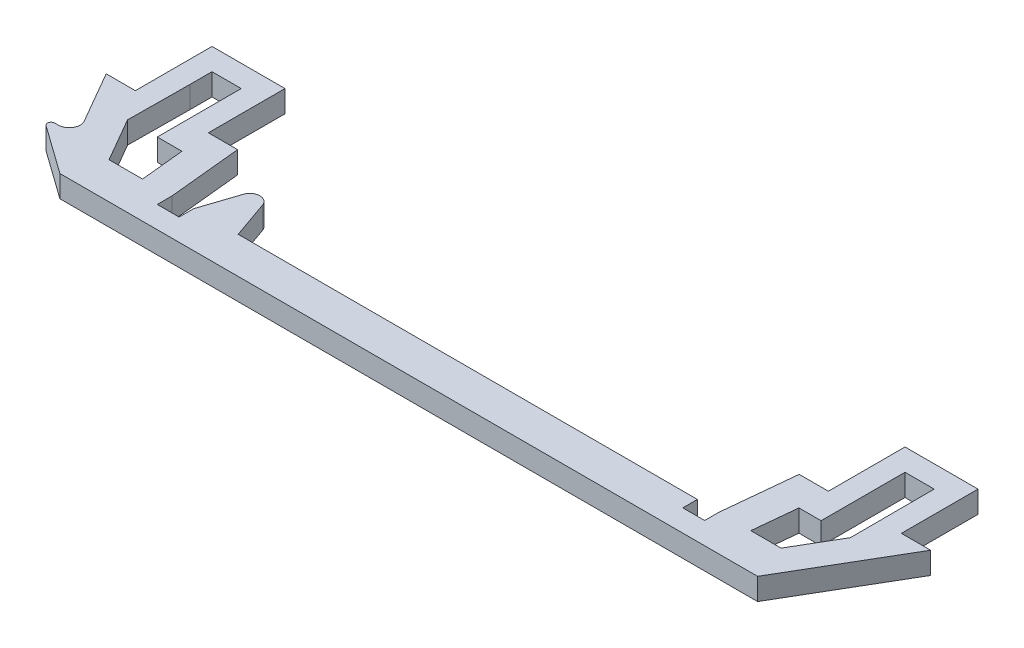
SolidWorks part; units mm, degrees
material "Custom Plastic"
ref_plane "Front Plane" through (0, 0, 0) normal (0, 0, 1) x (1, 0, 0)
ref_plane "Top Plane" through (0, 0, 0) normal (0, 1, 0) x (1, 0, 0)
ref_plane "Right Plane" through (0, 0, 0) normal (1, 0, 0) x (0, 0, -1)
sketch "Sketch1" plane through (0, 0, 0) normal (0, 1, 0) x (1, 0, 0)
  line L0 (-62.4186, -48.6587) -> (-58.4186, -48.6587)
  line L1 (-58.4186, -48.6587) -> (-58.4186, -38.1587)
  line L2 (-58.4186, -38.1587) -> (-48.4186, -38.1587)
  line L3 (-48.4186, -38.1587) -> (-48.4186, -48.6587)
  line L4 (-48.4186, -48.6587) -> (-44.4186, -48.6587)
  line L5 (-44.4186, -48.6587) -> (-43.4188, -58.6562)
  line L7 (31.5814, -58.7088) -> (32.5814, -48.7113)
  line L8 (32.5814, -48.7113) -> (36.5814, -48.7113)
  line L9 (36.5814, -48.7113) -> (36.5814, -38.2113)
  line L10 (36.5814, -38.2113) -> (46.5814, -38.2113)
  line L11 (46.5814, -38.2113) -> (46.5814, -48.7113)
  line L12 (46.5814, -48.7113) -> (50.5814, -48.7113)
  line L13 (50.5814, -48.7113) -> (41.8306, -63.6587)
  line L14 (41.8306, -63.6587) -> (-53.7583, -63.6587)
  line L15 (-58.3105, -55.774) -> (-62.4186, -48.6587)
  line L16 (36.5478, -52.7113) -> (39.5814, -52.7113)
  line L17 (-55.4186, -41.1587) -> (-51.4186, -41.1587)
  line L18 (-55.4186, -41.1587) -> (-55.4186, -44.1587)
  line L20 (-51.4186, -41.1587) -> (-51.4186, -44.1587)
  line L21 (39.5814, -41.2113) -> (43.5814, -41.2113)
  line L22 (39.5814, -41.2113) -> (39.5814, -44.2113)
  line L24 (43.5814, -41.2113) -> (43.5814, -44.2113)
  line L25 (43.6046, -52.7113) -> (40.0934, -58.7088)
  line L26 (40.0934, -58.7088) -> (35.9479, -58.7088)
  line L27 (35.9479, -58.7088) -> (36.5478, -52.7113)
  line L28 (-51.4186, -52.6587) -> (-48.0385, -52.6587)
  line L29 (-48.0385, -52.6587) -> (-47.4385, -58.6587)
  line L30 (-47.4385, -58.6587) -> (-52.0263, -58.6587)
  line L31 (-52.0263, -58.6587) -> (-55.4904, -52.6587)
  line L32 (28.5814, -58.6587) -> (28.5814, -60.6587)
  line L33 (28.5814, -48.6587) -> (28.5814, -63.6587) construction
  line L34 (28.5814, -60.6587) -> (31.5814, -60.6587)
  line L35 (31.5814, -60.6587) -> (31.5814, -58.7088)
  line L36 (31.5814, -63.6587) -> (31.5814, -48.6587) construction
  line L38 (-43.4188, -58.6562) -> (-43.4188, -60.6587)
  line L39 (-43.4188, -60.6587) -> (-40.4188, -60.6587)
  line L40 (-40.4188, -60.6587) -> (-40.4188, -58.6587)
  line L41 (-34.3352, -58.6587) -> (28.5814, -58.6587)
  line L42 (-34.3352, -58.6587) -> (-36.1291, -53.5241)
  line L43 (43.5814, -44.2113) -> (43.6046, -52.7113)
  line L44 (-38.7227, -53.5447) -> (-40.4188, -58.6587)
  line L45 (39.5814, -44.2113) -> (39.5814, -52.7113)
  line L46 (-55.4186, -44.1587) -> (-55.4904, -52.6587)
  line L47 (-51.4186, -44.1587) -> (-51.4186, -52.6587)
  line L48 (-53.7583, -63.6587) -> (-60.3821, -58.931)
  line L49 (-60.0916, -58.024) -> (-59.6096, -58.024)
  arc A0 (-38.7227, -53.5447) -> (-36.1291, -53.5241) centre (-37.4224, -53.9759) cw
  arc A1 (-59.6096, -58.024) -> (-58.3105, -55.774) centre (-59.6096, -56.524) ccw
  arc A2 (-60.3821, -58.931) -> (-60.0916, -58.024) centre (-60.0916, -58.524) cw
  dimension "D6" = 0.5
  dimension "D5" = 1.5
  dimension "D1" = 15
  dimension "D2" = 4
  dimension "D3" = 10.5
  dimension "D4" = 3
  dimension "D7" = 120
  dimension "D8" = 10
  dimension "D9" = 85
  dimension "D10" = 3
  dimension "D12" = 3
  dimension "D13" = 3
  dimension "D14" = 3
  dimension "D15" = 3
  dimension "D17" = 4
  dimension "D18" = 4
  dimension "D19" = 4
  dimension "D20" = 4
  dimension "D21" = 4
  dimension "D23" = 2
  dimension "D24" = 3
extrude "Boss-Extrude1" add sketch "Sketch1" along normal blind 3
